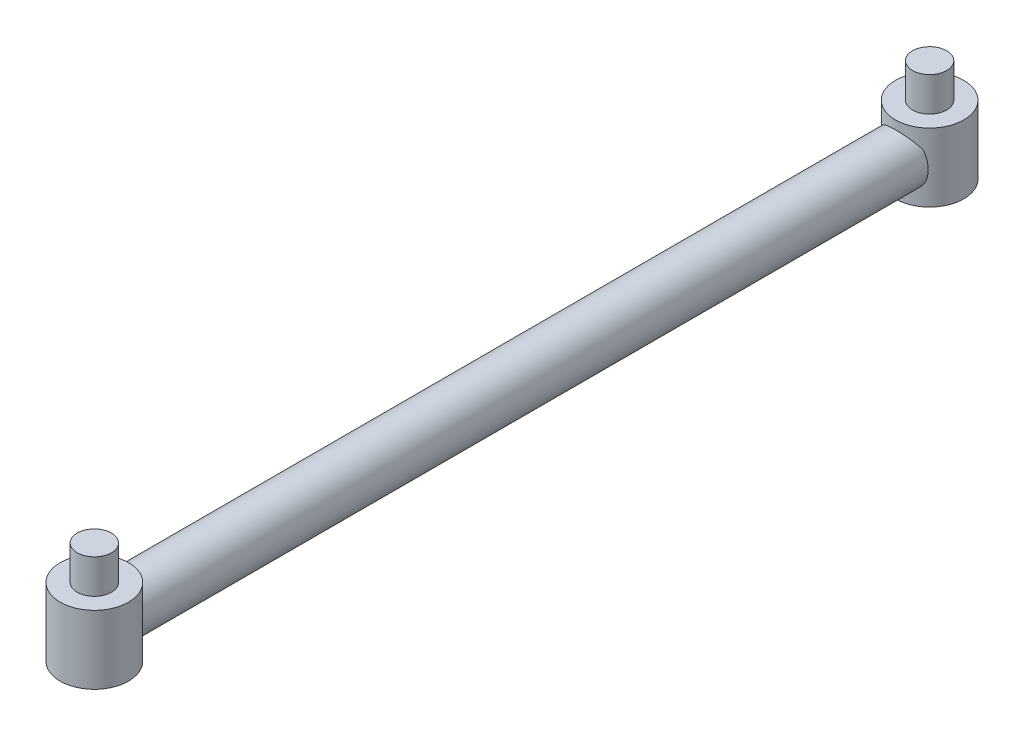
SolidWorks part; units mm, degrees
ref_plane "Ebene vorne" through (0, 0, 0) normal (0, 0, 1) x (1, 0, 0)
ref_plane "Ebene oben" through (0, 0, 0) normal (0, 1, 0) x (1, 0, 0)
ref_plane "Ebene rechts" through (0, 0, 0) normal (1, 0, 0) x (0, 0, -1)
sketch "Skizze1" plane through (0, 0, 0) normal (0, 0, 1) x (1, 0, 0)
  circle A0 centre (0, 0) radius 1.5
extrude "Aufsatz-Linear austragen1" add sketch "Skizze1" along normal blind 46
sketch "Skizze2" plane through (0, 0, 0) normal (0, 1, 0) x (1, 0, 0)
  circle A0 centre (0, -47.238) radius 2
  circle A2 centre (0, 1.5818) radius 2
extrude "Aufsatz-Linear austragen2" add sketch "Skizze2" against normal blind 4 from offset 2
sketch "Skizze3" plane through (0, 2, 0) normal (0, 1, 0) x (1, 0, 0)
  circle A0 centre (0, -47.238) radius 1
  circle A2 centre (0, 1.5818) radius 1
extrude "Aufsatz-Linear austragen4" add sketch "Skizze3" along normal blind 2
